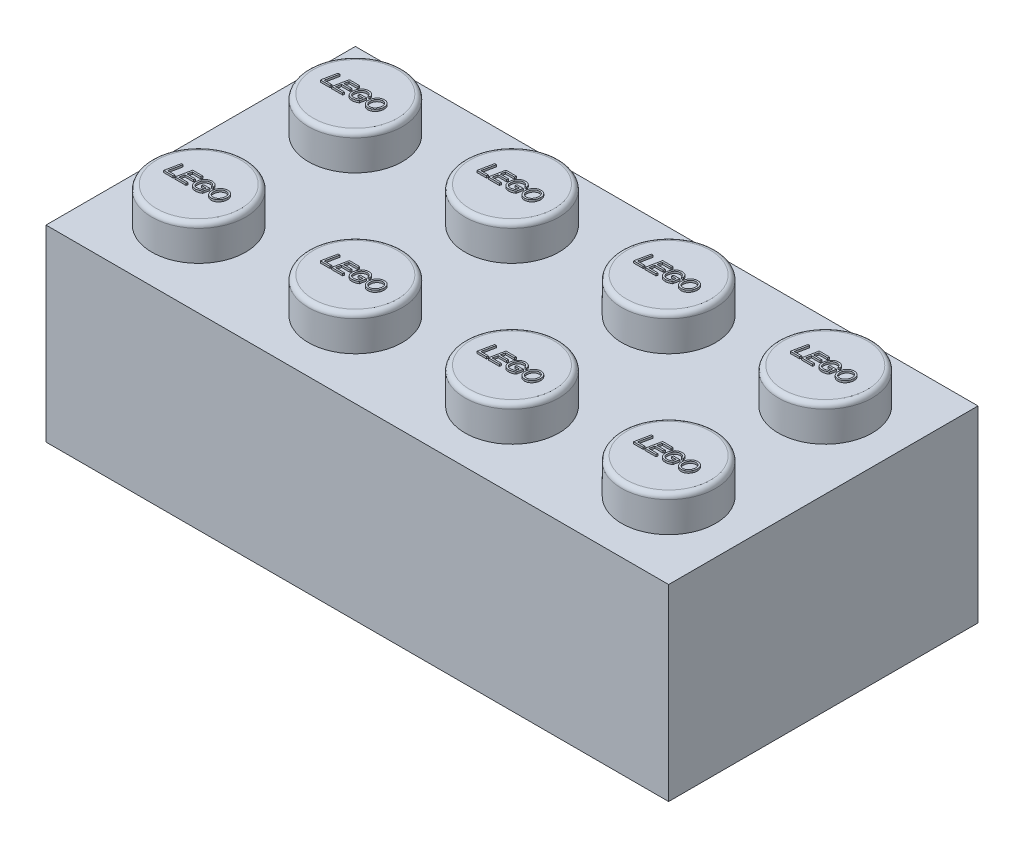
SolidWorks part; units mm, degrees
material "ABS"
ref_plane "Front Plane" through (0, 0, 0) normal (0, 0, 1) x (1, 0, 0)
ref_plane "Top Plane" through (0, 0, 0) normal (0, 1, 0) x (1, 0, 0)
ref_plane "Right Plane" through (0, 0, 0) normal (1, 0, 0) x (0, 0, -1)
sketch "Sketch1" plane through (0, 0, 0) normal (0, 1, 0) x (1, 0, 0)
  line L1 (0, 0) -> (31.8, 0)
  line L2 (0, 0) -> (0, 15.8)
  line L3 (0, 15.8) -> (31.8, 15.8)
  line L4 (31.8, 0) -> (31.8, 15.8)
  dimension "D1" = 15.8
  dimension "D2" = 31.8
extrude "Boss-Extrude1" add sketch "Sketch1" along normal blind 9.6
sketch "Sketch2" plane through (0, 9.6, 0) normal (0, 1, 0) x (1, 0, 0)
  line L0 (0, 15.8) -> (0, 0) construction
  line L1 (31.8, 15.8) -> (0, 15.8) construction
  circle A0 centre (3.9, 11.9) radius 2.4
  circle A1 centre (11.9, 11.9) radius 2.4
  circle A2 centre (27.9, 11.9) radius 2.4
  circle A3 centre (19.9, 11.9) radius 2.4
  circle A4 centre (3.9, 3.9) radius 2.4
  circle A5 centre (11.9, 3.9) radius 2.4
  circle A7 centre (27.9, 3.9) radius 2.4
  circle A8 centre (19.9, 3.9) radius 2.4
  dimension "D1" = 4.8
  dimension "D12" = 3.9
  dimension "D13" = 3.9
  dimension "D14" = 3.9
  dimension "D15" = 3.9
  dimension "D2" = 8
  dimension "D3" = 8
  dimension "D4" = 8
  dimension "D5" = 8
  dimension "D6" = 8
  dimension "D7" = 8
  dimension "D8" = 8
  dimension "D9" = 8
  dimension "D10" = 8
  dimension "D11" = 8
extrude "Boss-Extrude2" add sketch "Sketch2" along normal blind 1.8
shell "Shell1" thickness 1.2
sketch "Sketch3" plane through (0, 8.4, 0) normal (0, -1, 0) x (1, 0, 0)
  line L0 (1.2, -7.9) -> (30.6, -7.9) construction
  line L1 (1.2, -14.6) -> (1.2, -1.2) construction
  line L2 (30.6, -1.2) -> (30.6, -14.6) construction
  line L3 (27.9, -3.9) -> (19.9, -11.9) construction
  line L4 (3.9, -3.9) -> (11.9, -11.9) construction
  circle A0 centre (7.9, -7.9) radius 3.25
  circle A1 centre (15.9, -7.9) radius 3.25
  circle A2 centre (23.9, -7.9) radius 3.25
  circle A3 centre (7.9, -7.9) radius 2.4
  circle A4 centre (15.9, -7.9) radius 2.4
  circle A5 centre (23.9, -7.9) radius 2.4
  dimension "D1" = 6.5
  dimension "D2" = 4.8
extrude "Boss-Extrude3" add sketch "Sketch3" along normal up to surface (8.4 mm away) up to face at (15.9, 0, -7.9)
sketch "Sketch5" plane through (0, 11.4, 0) normal (0, 1, 0) x (1, 0, 0)
  text T0 "LEGO" font "Century Gothic" height 0.75
sketch "Sketch8" plane through (0, 9.6, 0) normal (0, 1, 0) x (1, 0, 0)
sketch "Sketch9" plane through (0, 11.4, 0) normal (0, 1, 0) x (1, 0, 0)
extrude "Boss-Extrude6" add sketch "Sketch5" along normal blind 0.1
fillet "Fillet1" radius 0.25 8 edges at (27.9, 11.4, -9.5) (19.9, 11.4, -1.5) (27.9, 11.4, -1.5) (19.9, 11.4, -9.5) (11.9, 11.4, -1.5) (3.9, 11.4, -1.5) (11.9, 11.4, -9.5) (3.9, 11.4, -9.5)
pattern_linear "LPattern1" count 4 spacing 8 along (1, 0, 0) count 2 spacing 8 along (0, 0, 1) of "Boss-Extrude6"
